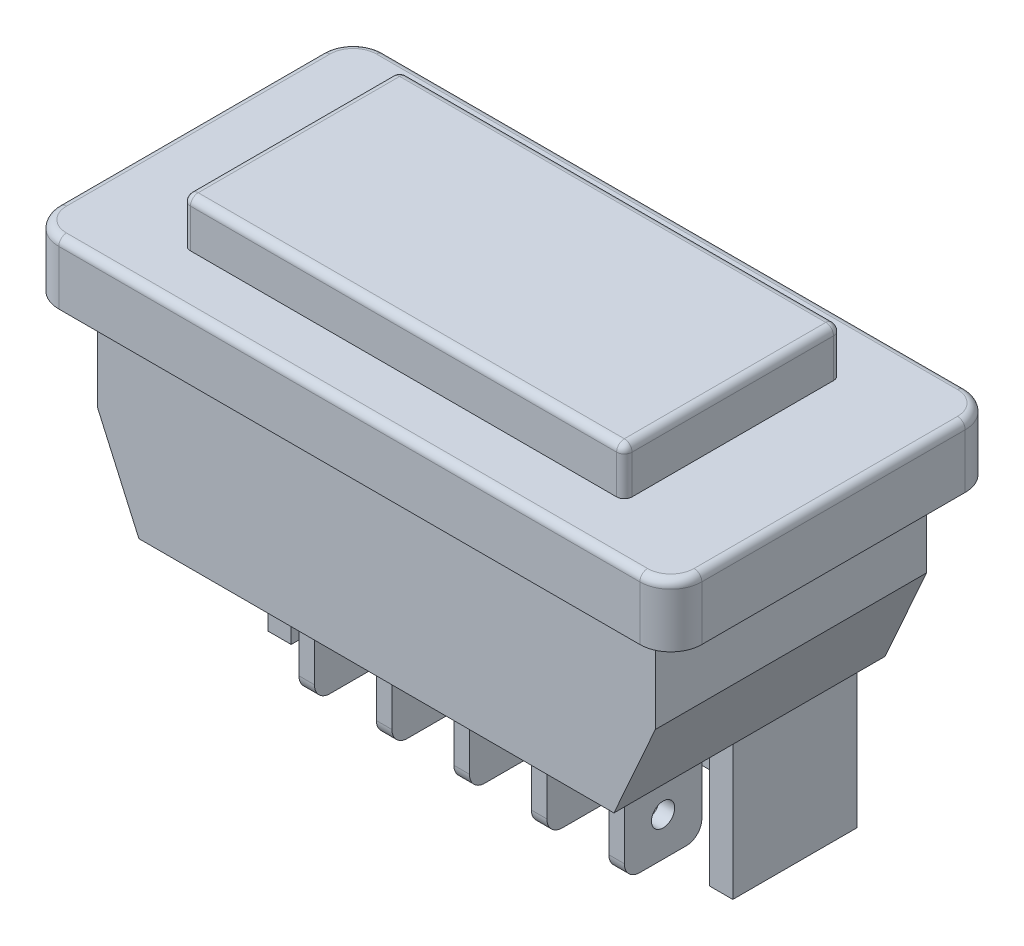
SolidWorks part; units mm, degrees
ref_plane "Спереди" through (0, 0, 0) normal (0, 0, 1) x (1, 0, 0)
ref_plane "Сверху" through (0, 0, 0) normal (0, 1, 0) x (1, 0, 0)
ref_plane "Справа" through (0, 0, 0) normal (1, 0, 0) x (0, 0, -1)
sketch "Эскиз1" plane through (0, 0, 0) normal (0, 1, 0) x (1, 0, 0)
  line L1 (-20.75, 10.5) -> (20.75, 10.5)
  line L2 (-20.75, 10.5) -> (-20.75, -10.5)
  line L3 (-20.75, -10.5) -> (20.75, -10.5)
  line L4 (20.75, 10.5) -> (20.75, -10.5)
  line L5 (-20.75, 10.5) -> (20.75, -10.5) construction
  line L6 (-20.75, -10.5) -> (20.75, 10.5) construction
  point P0 (0, 0)
  dimension "D1" = 41.5
  dimension "D2" = 21
extrude "Бобышка-Вытянуть1" add sketch "Эскиз1" along normal blind 4
fillet "Скругление1" radius 2 4 edges at (-20.75, 2, -10.5) (20.75, 2, -10.5) (20.75, 2, 10.5) (-20.75, 2, 10.5)
fillet "Скругление2" radius 0.5 8 edges at (20.1642, 4, -9.9142) (20.75, 4, 0) (20.1642, 4, 9.9142) (0, 4, 10.5) (-20.1642, 4, 9.9142) (-20.75, 4, 0) (-20.1642, 4, -9.9142) (0, 4, -10.5)
sketch "Эскиз2" plane through (0, 4, 0) normal (0, 1, 0) x (1, 0, 0)
  line L1 (-14.25, 7) -> (14.25, 7)
  line L2 (-14.25, 7) -> (-14.25, -7)
  line L3 (-14.25, -7) -> (14.25, -7)
  line L4 (14.25, 7) -> (14.25, -7)
  line L5 (-14.25, 7) -> (14.25, -7) construction
  line L6 (-14.25, -7) -> (14.25, 7) construction
  point P0 (0, 0)
  dimension "D1" = 14
  dimension "D2" = 28.5
extrude "Бобышка-Вытянуть2" add sketch "Эскиз2" along normal blind 3
fillet "Скругление3" radius 0.5 8 edges at (14.25, 7, 0) (0, 7, 7) (-14.25, 7, 0) (0, 7, -7) (14.25, 5.5, -7) (-14.25, 5.5, -7) (14.25, 5.5, 7) (-14.25, 5.5, 7)
sketch "Эскиз3" plane through (0, 0, 0) normal (0, -1, 0) x (1, 0, 0)
  line L1 (-18, 8.75) -> (18, 8.75)
  line L2 (-18, 8.75) -> (-18, -8.75)
  line L3 (-18, -8.75) -> (18, -8.75)
  line L4 (18, 8.75) -> (18, -8.75)
  line L5 (-18, 8.75) -> (18, -8.75) construction
  line L6 (-18, -8.75) -> (18, 8.75) construction
  point P0 (0, 0)
  dimension "D1" = 17.5
  dimension "D2" = 36
extrude "Бобышка-Вытянуть3" add sketch "Эскиз3" along normal blind 12
chamfer "Фаска1" distance 6 angle 24 2 edges at (18, -12, 0) (-18, -12, 0)
sketch "Эскиз4" plane through (0, -12, 0) normal (0, -1, 0) x (1, 0, 0)
  line L0 (13.5, 0.75) -> (15, 0.75)
  line L2 (-13.5, 0.75) -> (-13.5, -5.75)
  line L3 (-13.5, -5.75) -> (13.5, -5.75)
  line L4 (13.5, 0.75) -> (13.5, -5.75)
  line L5 (-11.5361, 11.0024) -> (13.5, -5.75) construction
  line L6 (-13.5, -5.75) -> (11.5361, 11.0024) construction
  line L7 (-15, 0.75) -> (-13.5, 0.75)
  line L8 (-15, 0.75) -> (-15, -7.25)
  line L9 (-15, -7.25) -> (15, -7.25)
  line L10 (15, 0.75) -> (15, -7.25)
  line L11 (-15, 0.75) -> (15, -7.25) construction
  line L12 (-15, -7.25) -> (15, 0.75) construction
  line L13 (-15.3286, -8.75) -> (15.3286, -8.75) construction
  line L14 (0, 8.75) -> (0, -9.1835) construction
  line L15 (15.3286, 8.75) -> (-15.3286, 8.75) construction
  line L16 (4.5, 3.25) -> (4.5, -1.75)
  line L17 (-0.5, 3.25) -> (0.5, 3.25)
  line L18 (-0.5, 3.25) -> (-0.5, -1.75)
  line L19 (-0.5, -1.75) -> (0.5, -1.75)
  line L20 (0.5, 3.25) -> (0.5, -1.75)
  line L21 (-0.5, 3.25) -> (0.5, -1.75) construction
  line L22 (-0.5, -1.75) -> (0.5, 3.25) construction
  line L23 (4.5, 3.25) -> (5.5, 3.25)
  line L24 (5.5, 3.25) -> (5.5, -1.75)
  line L25 (4.5, -1.75) -> (5.5, -1.75)
  line L26 (9.5, 3.25) -> (9.5, -1.75)
  line L27 (9.5, 3.25) -> (10.5, 3.25)
  line L28 (10.5, 3.25) -> (10.5, -1.75)
  line L29 (9.5, -1.75) -> (10.5, -1.75)
  line L30 (-5.5, 3.25) -> (-5.5, -1.75)
  line L31 (-5.5, 3.25) -> (-4.5, 3.25)
  line L32 (-4.5, 3.25) -> (-4.5, -1.75)
  line L33 (-5.5, -1.75) -> (-4.5, -1.75)
  line L34 (-10.5, 3.25) -> (-10.5, -1.75)
  line L35 (-10.5, 3.25) -> (-9.5, 3.25)
  line L36 (-9.5, 3.25) -> (-9.5, -1.75)
  line L37 (-10.5, -1.75) -> (-9.5, -1.75)
  line L38 (-0.5, 3.25) -> (-5.5, 3.25) construction
  line L39 (15.3286, -8.75) -> (15.3286, 8.75) construction
  point P0 (0, 3.2832)
  point P5 (0, -3.25)
  point P21 (0, 0.75)
  dimension "D1" = 1.5
  dimension "D2" = 1.5
  dimension "D3" = 30
  dimension "D4" = 1.5
  dimension "D5" = 8
  dimension "D6" = 1
  dimension "D7" = 5
  dimension "D10" = 5
  dimension "D11" = 4.8286
  dimension "D12" = 12.0332
  dimension "D13" = 19.7524
  dimension "D8" = 3
  dimension "D9" = 3
extrude "Бобышка-Вытянуть4" add sketch "Эскиз4" along normal blind 9
fillet "Скругление4" radius 1 10 edges at (-10, -21, -1.75) (-5, -21, -1.75) (0, -21, -1.75) (5, -21, -1.75) (10, -21, -1.75) (10, -21, 3.25) (5, -21, 3.25) (0, -21, 3.25) (-5, -21, 3.25) (-10, -21, 3.25)
sketch "Эскиз5" plane through (-10.5, 0, 0) normal (-1, 0, 0) x (0, 0, 1)
  line L0 (0.75, -21) -> (0.75, -12) construction
  line L1 (2.25, -21) -> (-0.75, -21) construction
  circle A0 centre (0.75, -18.5) radius 0.75
  dimension "D2" = 1.5
  dimension "D1" = 2.5
extrude "Вырез-Вытянуть1" cut sketch "Эскиз5" against normal up to surface (21 mm away) from surface at 0 up to face at (10.5, -17.7357, 0.75) starting at face at (-10.5, -17.7357, 0.75)
